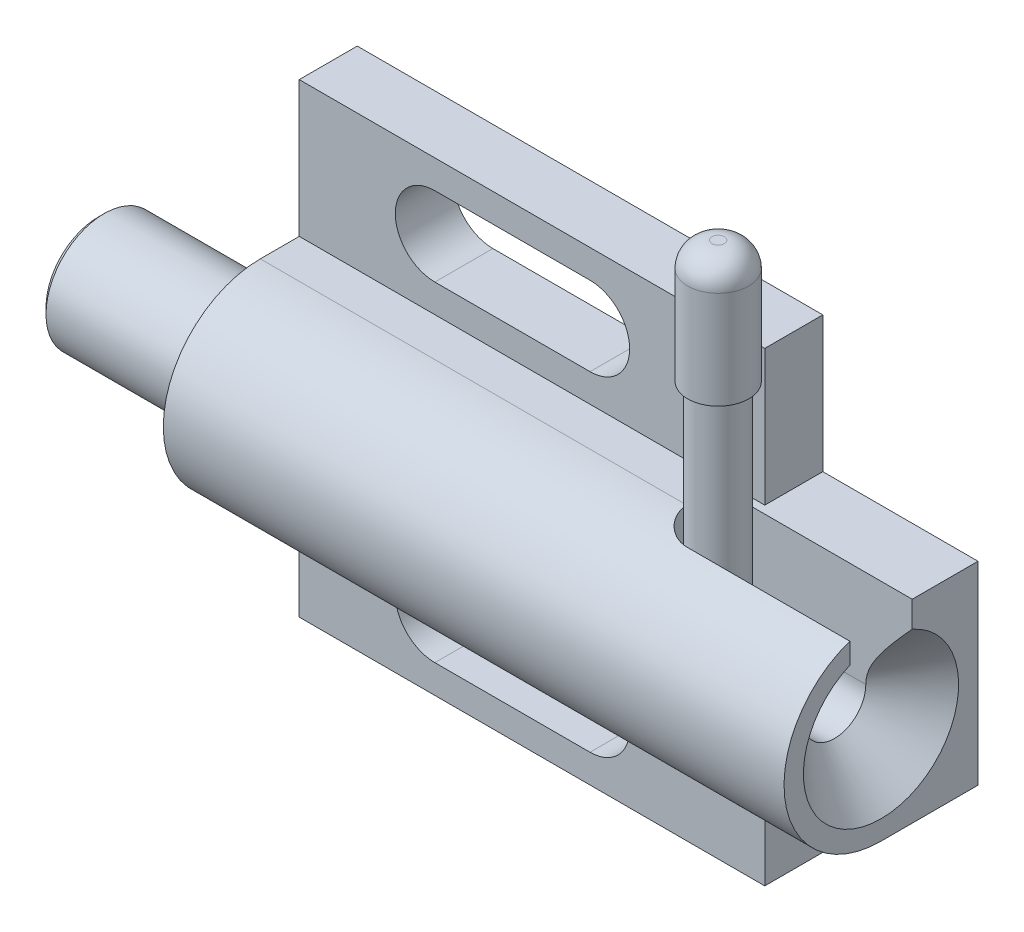
SolidWorks part; units mm, degrees
ref_plane "Front Plane" through (0, 0, 0) normal (0, 0, 1) x (1, 0, 0)
ref_plane "Top Plane" through (0, 0, 0) normal (0, 1, 0) x (1, 0, 0)
ref_plane "Right Plane" through (0, 0, 0) normal (1, 0, 0) x (0, 0, -1)
sketch "Sketch1" plane through (0, 0, 0) normal (1, 0, 0) x (0, 0, -1)
  line L0 (0, -19.05) -> (0, 19.05)
  line L3 (-4.7498, -19.05) -> (-4.7498, -7.9375)
  line L4 (-4.7498, 19.05) -> (0, 19.05)
  line L5 (0, -19.05) -> (-4.7498, -19.05)
  line L16 (-4.7498, 7.9375) -> (-4.7498, 19.05)
  line L17 (0, 0) -> (-15.875, 0) construction
  line L18 (-7.9375, 7.9375) -> (-4.7498, 7.9375)
  line L19 (-7.9375, -7.9375) -> (-4.7498, -7.9375)
  arc A10 (-7.9375, 7.9375) -> (-7.9375, -7.9375) centre (-7.9375, 0) ccw
  circle A12 centre (-7.9375, 0) radius 7.9375 construction
  dimension "D1" = 38.1
  dimension "D2" = 15.875
  dimension "D3" = 4.7498
ref_plane "Plane1" through (25.4, 0, 0) normal (1, 0, 0) x (0, 0, -1)
sketch "Sketch4" plane through (25.4, 0, 0) normal (1, 0, 0) x (0, 0, -1)
  line L7 (0, -19.05) -> (0, 19.05)
  line L8 (0, 19.05) -> (-4.7498, 19.05)
  line L9 (-4.7498, 19.05) -> (-4.7498, 7.9375)
  line L10 (-4.7498, 7.9375) -> (-7.9375, 7.9375)
  line L11 (-7.9375, -7.9375) -> (-4.7498, -7.9375)
  line L12 (-4.7498, -7.9375) -> (-4.7498, -19.05)
  line L13 (-4.7498, -19.05) -> (0, -19.05)
  line L14 (0, -19.05) -> (0, 19.05)
  line L15 (0, 19.05) -> (-4.7498, 19.05)
  line L16 (-4.7498, 19.05) -> (-4.7498, 7.9375)
  line L17 (-4.7498, 7.9375) -> (-7.9375, 7.9375)
  line L18 (-7.9375, -7.9375) -> (-4.7498, -7.9375)
  line L19 (-4.7498, -7.9375) -> (-4.7498, -19.05)
  line L20 (-4.7498, -19.05) -> (0, -19.05)
  arc A1 (-7.9375, 7.9375) -> (-7.9375, -7.9375) centre (-7.9375, 0) ccw
  arc A2 (-7.9375, 7.9375) -> (-7.9375, -7.9375) centre (-7.9375, 0) ccw
  dimension "D1" = 0
extrude "Boss-Extrude2" add sketch "Sketch4" along normal blind 50.8 separate body
sketch "Sketch5" plane through (76.2, 0, 0) normal (1, 0, 0) x (0, 0, -1)
  line L1 (0, 19.05) -> (-4.7498, 19.05)
  line L2 (0, 19.05) -> (0, 7.9375)
  line L3 (0, 7.9375) -> (-4.7498, 7.9375)
  line L4 (-4.7498, 19.05) -> (-4.7498, 7.9375)
  line L5 (0, -19.05) -> (-4.7498, -19.05)
  line L6 (0, -19.05) -> (0, -7.9375)
  line L7 (0, -7.9375) -> (-4.7498, -7.9375)
  line L8 (-4.7498, -19.05) -> (-4.7498, -7.9375)
extrude "Cut-Extrude3" cut sketch "Sketch5" against normal blind 12.7
sketch "Sketch6" plane through (0, 0, 0) normal (0, 1, 0) x (1, 0, 0)
  line L0 (25.4, -7.9375) -> (76.2, -7.9375) construction
  line L1 (76.2, -15.875) -> (76.2, -7.9375) construction
  line L2 (25.4, -7.9375) -> (25.4, -13.8397)
  line L3 (25.4, -7.9375) -> (25.4, -15.875) construction
  line L4 (25.4, -13.8397) -> (26.4, -12.8397)
  line L5 (26.4, -12.8397) -> (57.15, -12.8397)
  line L6 (57.15, -12.8397) -> (58.5617, -10.4902)
  line L7 (58.5617, -10.4902) -> (72.4027, -10.4902)
  line L8 (72.4027, -10.4902) -> (76.2, -14.2875)
  line L9 (76.2, -7.9375) -> (76.2, -14.2875)
  line L10 (25.4, -7.9375) -> (76.2, -7.9375)
  dimension "D1" = 12.7
  dimension "D2" = 5.1054
  dimension "D3" = 45
  dimension "D4" = 59
  dimension "D5" = 9.8044
  dimension "D6" = 1
  dimension "D7" = 45
  dimension "D8" = 31.75
revolve "Cut-Revolve2" cut sketch "Sketch6" angle 360 mid plane about L0
sketch "Sketch7" plane through (0, 0, 0) normal (0, 1, 0) x (1, 0, 0)
  line L0 (76.2, -7.9375) -> (60.3225, -7.9375) construction
  line L1 (62.8752, -10.4902) -> (76.2, -10.4902)
  line L2 (76.2, -7.9375) -> (76.2, -14.2875) construction
  line L3 (58.5617, -10.4902) -> (72.4027, -10.4902) construction
  line L4 (25.4, -7.9375) -> (76.2, -7.9375) construction
  line L5 (62.8752, -5.3848) -> (76.2, -5.3848)
  line L6 (76.2, -5.3848) -> (76.2, -10.4902)
  arc A0 (62.8752, -5.3848) -> (62.8752, -10.4902) centre (62.8752, -7.9375) ccw
  dimension "D1" = 15.8775
extrude "Cut-Extrude4" cut sketch "Sketch7" along normal up to next
sketch "Sketch8" plane through (0, 0, 0) normal (0, 0, 1) x (1, 0, 0)
  line L0 (36.4998, 13.4874) -> (49.1998, 13.4874) construction
  line L1 (36.4998, 16.7259) -> (49.1998, 16.7259)
  line L2 (36.4998, 10.2489) -> (49.1998, 10.2489)
  line L3 (25.4, 0) -> (76.2, 0) construction
  line L4 (76.2, -7.9375) -> (76.2, 7.9375) construction
  line L5 (36.4998, -13.4874) -> (49.1998, -13.4874) construction
  line L6 (36.4998, -16.7259) -> (49.1998, -16.7259)
  line L7 (36.4998, -10.2489) -> (49.1998, -10.2489)
  line L9 (63.5, 19.05) -> (63.5, 7.9375) construction
  arc A0 (36.4998, 16.7259) -> (36.4998, 10.2489) centre (36.4998, 13.4874) ccw
  arc A1 (49.1998, 10.2489) -> (49.1998, 16.7259) centre (49.1998, 13.4874) ccw
  arc A2 (36.4998, -16.7259) -> (36.4998, -10.2489) centre (36.4998, -13.4874) cw
  arc A3 (49.1998, -10.2489) -> (49.1998, -16.7259) centre (49.1998, -13.4874) cw
  point P2 (42.8498, 13.4874)
  point P14 (42.8498, -13.4874)
  dimension "D1" = 6.477
  dimension "D2" = 12.7
  dimension "D3" = 14.3002
  dimension "D4" = 26.9748
  dimension "D5" = 11.0998
extrude "Cut-Extrude5" cut sketch "Sketch8" along normal up to next
ref_plane "Plane2" through (0, 0, 7.9375) normal (0, 0, 1) x (1, 0, 0)
sketch "Sketch9" plane through (0, 0, 7.9375) normal (0, 0, 1) x (1, 0, 0)
  line L0 (12.1252, 0) -> (60.3752, 0) construction
  line L1 (62.8752, 2.5) -> (62.8752, 28) construction
  line L2 (60.8752, 28) -> (64.8752, 28) construction
  line L3 (12.1252, 0) -> (12.1252, 4.2625)
  line L4 (12.1252, 4.2625) -> (12.6252, 4.7625)
  line L5 (12.6252, 4.7625) -> (41.6252, 4.7625)
  line L6 (41.6252, 4.7625) -> (41.6252, 2)
  line L7 (41.6252, 2) -> (60.3752, 2)
  line L8 (60.3752, 2) -> (60.3752, 0)
  line L9 (41.6252, 2) -> (41.6252, -2) construction
  line L10 (12.1252, 0) -> (60.3752, 0)
  line L11 (25.4, 7.9375) -> (25.4, -7.9375) construction
  arc A0 (60.3752, 0) -> (62.8752, 2.5) centre (60.3752, 2.5) ccw construction
  point P3 (41.6252, 0)
  point P10 (62.8752, 0)
  dimension "D5" = 2.5
  dimension "D1" = 50.75
  dimension "D2" = 28
  dimension "D3" = 29.5
  dimension "D4" = 4
  dimension "D6" = 9.525
  dimension "D7" = 0.5
  dimension "D8" = 45
  dimension "D9" = 13.2748
revolve "Revolve1" add sketch "Sketch9" angle 360 mid plane about L10
sketch "Sketch11" plane through (0, 0, 7.9375) normal (0, 0, 1) x (1, 0, 0)
  line L0 (60.8752, 2.5) -> (60.8752, 18)
  line L1 (60.8752, 2.5) -> (62.8752, 2.5)
  line L2 (62.8752, 28) -> (62.3752, 28)
  line L3 (60.8752, 28) -> (64.8752, 28) construction
  line L4 (60.3752, 26) -> (60.3752, 18)
  line L5 (60.8752, 18) -> (60.3752, 18)
  line L6 (62.8752, 2.5) -> (62.8752, 28) construction
  line L7 (62.8752, 28) -> (62.8752, 2.5)
  arc A0 (62.3752, 28) -> (60.3752, 26) centre (62.3752, 26) ccw
  dimension "D3" = 2
  dimension "D1" = 5
  dimension "D2" = 10
revolve "Revolve2" add sketch "Sketch11" angle 360 mid plane about L6
sketch "Sketch12" plane through (60.3752, 0, 0) normal (1, 0, 0) x (0, 0, -1)
  circle A1 centre (-7.9375, 0) radius 2
  circle A2 centre (-7.9375, 0) radius 2
  dimension "D1" = 0
sketch "Sketch13" plane through (0, 0, 7.9375) normal (0, 0, 1) x (1, 0, 0)
  arc A0 (60.3752, 0) -> (62.8752, 2.5) centre (60.3752, 2.5) ccw construction
  arc A1 (60.3752, 0) -> (62.8752, 2.5) centre (60.3752, 2.5) ccw
sweep "Sweep1" add profiles "Sketch12" path "Sketch13"
